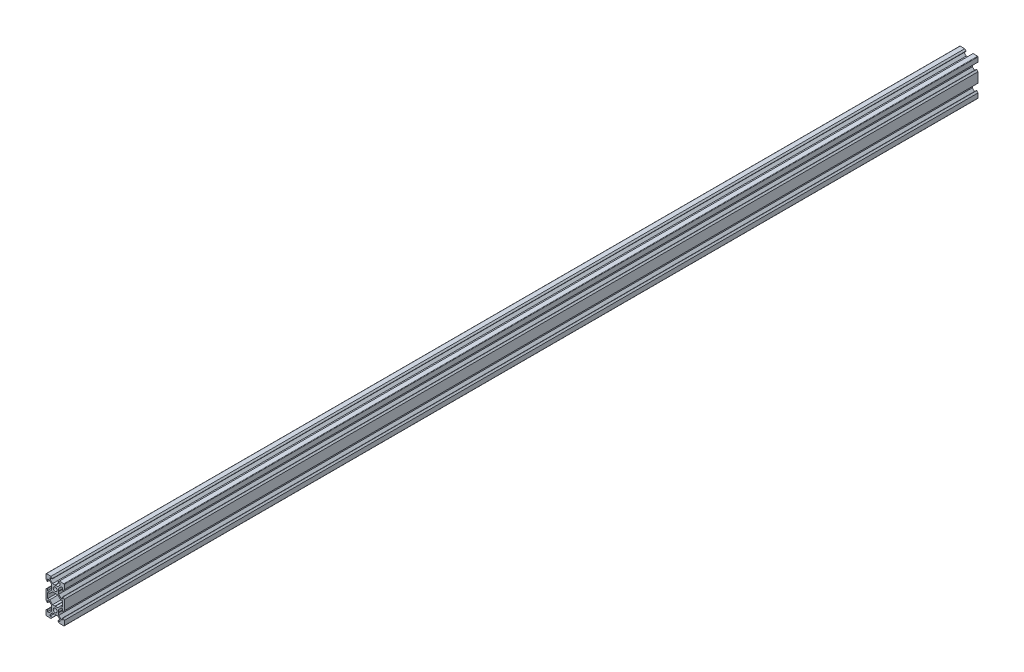
SolidWorks part; units mm, degrees
ref_plane "Front Plane" through (0, 0, 0) normal (0, 0, 1) x (1, 0, 0)
ref_plane "Top Plane" through (0, 0, 0) normal (0, 1, 0) x (1, 0, 0)
ref_plane "Right Plane" through (0, 0, 0) normal (1, 0, 0) x (0, 0, -1)
sketch "Sketch1" plane through (0, 0, 0) normal (0, 0, 1) x (1, 0, 0)
  line L0 (0, 0) -> (0, 20243.958) construction
  line L1 (0, 0) -> (20243.958, 0) construction
  line L2 (-10, 0) -> (10, 20) construction
  line L3 (-10, -20) -> (10, -20) construction
  line L4 (-10, -20) -> (-10, 20) construction
  line L5 (-10, 20) -> (10, 20) construction
  line L6 (10, -20) -> (10, 20) construction
  line L7 (0, 20) -> (0, -20) construction
  line L8 (-10, 0) -> (10, 0) construction
  line L9 (10, 0) -> (-10, 20) construction
  line L10 (10, 0) -> (-10, -20) construction
  line L11 (10, -20) -> (-10, 0) construction
  line L12 (10, 10) -> (-10, 10) construction
  line L14 (2.8393, 13.9) -> (5.5, 16.5607)
  line L15 (5.5, 16.5607) -> (5.5, 18.2)
  line L16 (5.5, 18.2) -> (3.125, 18.2)
  line L17 (3.125, 18.2) -> (3.125, 18.545)
  line L18 (3.125, 18.545) -> (4.58, 20)
  line L19 (4.58, 20) -> (10, 20)
  line L20 (10, 20) -> (10, 14.58)
  line L21 (10, 14.58) -> (8.545, 13.125)
  line L22 (8.545, 13.125) -> (8.2, 13.125)
  line L23 (8.2, 13.125) -> (8.2, 15.5)
  line L24 (8.2, 15.5) -> (6.5607, 15.5)
  line L25 (6.5607, 15.5) -> (3.9, 12.8393)
  line L26 (0, 13.7) -> (0.2, 13.9)
  line L27 (0.2, 13.9) -> (2.8393, 13.9)
  line L28 (3.9, 12.8393) -> (3.9, 10.2)
  line L29 (3.9, 10.2) -> (3.7, 10)
  line L30 (3.7, 10) -> (3.9, 9.8)
  line L31 (3.9, 9.8) -> (3.9, 7.1607)
  line L32 (3.9, 7.1607) -> (6.5607, 4.5)
  line L33 (6.5607, 4.5) -> (8.2, 4.5)
  line L34 (8.2, 4.5) -> (8.2, 6.875)
  line L35 (8.2, 6.875) -> (8.545, 6.875)
  line L36 (8.545, 6.875) -> (10, 5.42)
  line L37 (10, 5.42) -> (10, -5.42)
  line L38 (8.2, -3) -> (8.2, 3)
  line L39 (8.2, 3) -> (5.9393, 3)
  line L40 (5.9393, 3) -> (2.8393, 6.1)
  line L41 (2.8393, 6.1) -> (0.2, 6.1)
  line L42 (0.2, 6.1) -> (0, 6.3)
  line L43 (-5.9393, 3) -> (-2.8393, 6.1)
  line L44 (-0.2, 6.1) -> (0, 6.3)
  line L45 (-2.8393, 6.1) -> (-0.2, 6.1)
  line L46 (-8.2, 3) -> (-5.9393, 3)
  line L47 (-8.2, -3) -> (-8.2, 3)
  line L48 (-10, 5.42) -> (-10, -5.42)
  line L49 (-8.545, 6.875) -> (-10, 5.42)
  line L50 (-8.2, 4.5) -> (-8.2, 6.875)
  line L51 (-6.5607, 4.5) -> (-8.2, 4.5)
  line L52 (-8.2, 6.875) -> (-8.545, 6.875)
  line L53 (-3.9, 7.1607) -> (-6.5607, 4.5)
  line L54 (-3.9, 9.8) -> (-3.9, 7.1607)
  line L55 (-3.7, 10) -> (-3.9, 9.8)
  line L56 (-3.9, 10.2) -> (-3.7, 10)
  line L57 (-3.9, 12.8393) -> (-3.9, 10.2)
  line L58 (-6.5607, 15.5) -> (-3.9, 12.8393)
  line L59 (-8.2, 15.5) -> (-6.5607, 15.5)
  line L60 (-8.2, 13.125) -> (-8.2, 15.5)
  line L61 (-8.545, 13.125) -> (-8.2, 13.125)
  line L62 (-10, 14.58) -> (-8.545, 13.125)
  line L63 (-10, 20) -> (-10, 14.58)
  line L64 (-4.58, 20) -> (-10, 20)
  line L65 (-3.125, 18.545) -> (-4.58, 20)
  line L66 (-3.125, 18.2) -> (-3.125, 18.545)
  line L67 (-5.5, 18.2) -> (-3.125, 18.2)
  line L68 (-5.5, 16.5607) -> (-5.5, 18.2)
  line L69 (-2.8393, 13.9) -> (-5.5, 16.5607)
  line L70 (-0.2, 13.9) -> (-2.8393, 13.9)
  line L71 (0, 13.7) -> (-0.2, 13.9)
  line L72 (10, -10) -> (-10, -10) construction
  line L73 (10, 0) -> (-10, -20) construction
  line L74 (-10, -20) -> (10, -20) construction
  line L75 (-10, 0) -> (10, -20) construction
  line L76 (0, -13.7) -> (-0.2, -13.9)
  line L77 (-0.2, -13.9) -> (-2.8393, -13.9)
  line L78 (-2.8393, -13.9) -> (-5.5, -16.5607)
  line L79 (-5.5, -16.5607) -> (-5.5, -18.2)
  line L80 (-5.5, -18.2) -> (-3.125, -18.2)
  line L81 (-3.125, -18.2) -> (-3.125, -18.545)
  line L82 (-3.125, -18.545) -> (-4.58, -20)
  line L83 (-4.58, -20) -> (-10, -20)
  line L84 (-10, -20) -> (-10, -14.58)
  line L85 (-10, -14.58) -> (-8.545, -13.125)
  line L86 (-8.545, -13.125) -> (-8.2, -13.125)
  line L87 (-8.2, -13.125) -> (-8.2, -15.5)
  line L88 (-8.2, -15.5) -> (-6.5607, -15.5)
  line L89 (-6.5607, -15.5) -> (-3.9, -12.8393)
  line L90 (-3.9, -12.8393) -> (-3.9, -10.2)
  line L91 (-3.9, -10.2) -> (-3.7, -10)
  line L92 (-3.7, -10) -> (-3.9, -9.8)
  line L93 (-3.9, -9.8) -> (-3.9, -7.1607)
  line L94 (-3.9, -7.1607) -> (-6.5607, -4.5)
  line L95 (-8.2, -6.875) -> (-8.545, -6.875)
  line L96 (-6.5607, -4.5) -> (-8.2, -4.5)
  line L97 (-8.2, -4.5) -> (-8.2, -6.875)
  line L98 (-8.545, -6.875) -> (-10, -5.42)
  line L99 (-8.2, -3) -> (-5.9393, -3)
  line L100 (-2.8393, -6.1) -> (-0.2, -6.1)
  line L101 (-0.2, -6.1) -> (0, -6.3)
  line L102 (-5.9393, -3) -> (-2.8393, -6.1)
  line L103 (0.2, -6.1) -> (0, -6.3)
  line L104 (2.8393, -6.1) -> (0.2, -6.1)
  line L105 (5.9393, -3) -> (2.8393, -6.1)
  line L106 (8.2, -3) -> (5.9393, -3)
  line L107 (8.545, -6.875) -> (10, -5.42)
  line L108 (8.2, -6.875) -> (8.545, -6.875)
  line L109 (8.2, -4.5) -> (8.2, -6.875)
  line L110 (6.5607, -4.5) -> (8.2, -4.5)
  line L111 (3.9, -7.1607) -> (6.5607, -4.5)
  line L112 (3.9, -9.8) -> (3.9, -7.1607)
  line L113 (3.7, -10) -> (3.9, -9.8)
  line L114 (3.9, -10.2) -> (3.7, -10)
  line L115 (3.9, -12.8393) -> (3.9, -10.2)
  line L116 (0.2, -13.9) -> (2.8393, -13.9)
  line L117 (0, -13.7) -> (0.2, -13.9)
  line L118 (6.5607, -15.5) -> (3.9, -12.8393)
  line L119 (8.2, -15.5) -> (6.5607, -15.5)
  line L120 (8.2, -13.125) -> (8.2, -15.5)
  line L121 (8.545, -13.125) -> (8.2, -13.125)
  line L122 (10, -14.58) -> (8.545, -13.125)
  line L123 (10, -20) -> (10, -14.58)
  line L124 (4.58, -20) -> (10, -20)
  line L125 (3.125, -18.545) -> (4.58, -20)
  line L126 (3.125, -18.2) -> (3.125, -18.545)
  line L127 (5.5, -18.2) -> (3.125, -18.2)
  line L128 (5.5, -16.5607) -> (5.5, -18.2)
  line L129 (2.8393, -13.9) -> (5.5, -16.5607)
  circle A0 centre (0, 10) radius 2.1
  circle A1 centre (0, -10) radius 2.1
  point P5 (0, 0)
  point P101 (-8.2, 0)
  point P109 (8.2, 0)
  dimension "D15" = 4.2
  dimension "D1" = 40
  dimension "D2" = 20
  dimension "D3" = 4.58
  dimension "D4" = 1.8
  dimension "D5" = 3.125
  dimension "D6" = 135
  dimension "D7" = 1.5
  dimension "D8" = 4.3
  dimension "D9" = 0.2
  dimension "D10" = 0.2
  dimension "D11" = 5.5
  dimension "D12" = 135
  dimension "D13" = 1.5
  dimension "D14" = 1.5
extrude "Boss-Extrude1" add sketch "Sketch1" along normal mid plane 1000
fillet "Fillet1" radius 0.5 4 edges at (-10, -20, 0) (10, -20, 0) (-10, 20, 0) (10, 20, 0)
ref_plane "Plane1" [suppressed] through (0, 10, 0) normal (0, 1, 0) x (1, 0, 0)
